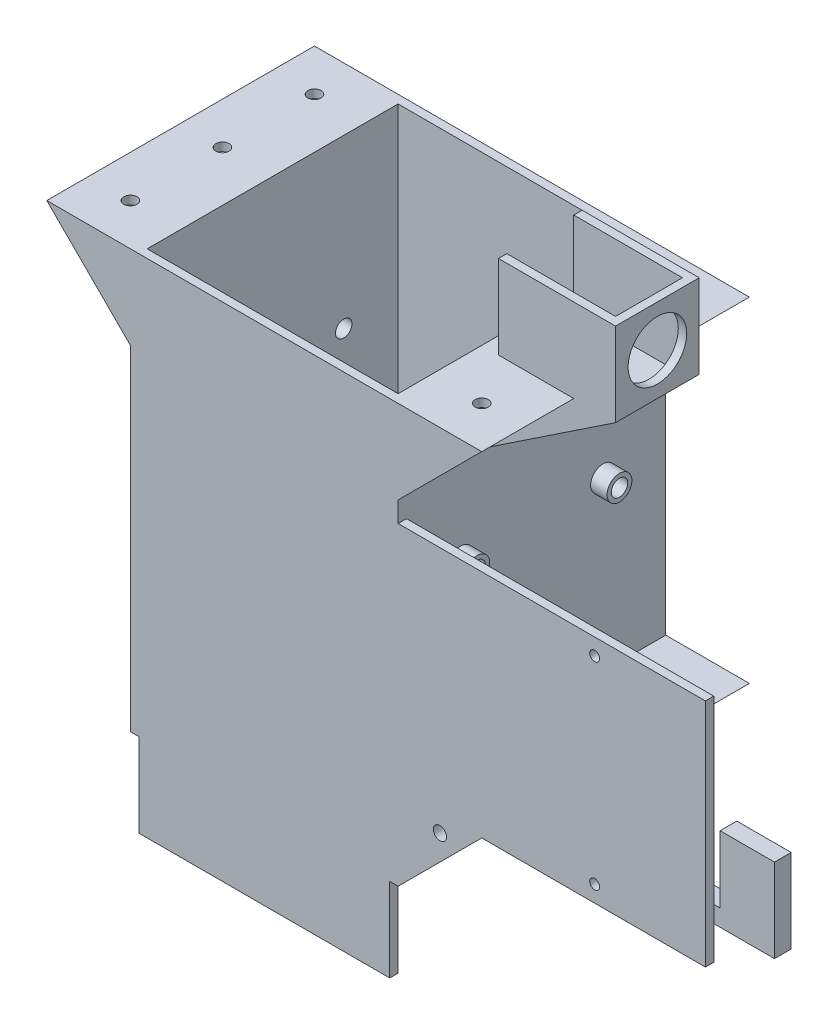
SolidWorks part; units mm, degrees
ref_plane "Front Plane" through (0, 0, 0) normal (0, 0, 1) x (1, 0, 0)
ref_plane "Top Plane" through (0, 0, 0) normal (0, 1, 0) x (1, 0, 0)
ref_plane "Right Plane" through (0, 0, 0) normal (1, 0, 0) x (0, 0, -1)
sketch "Sketch1" plane through (0, 0, 0) normal (0, 1, 0) x (1, 0, 0)
  line L1 (0, 0) -> (81.28, 0)
  line L2 (0, 0) -> (0, 81.28)
  line L3 (0, 81.28) -> (81.28, 81.28)
  line L4 (81.28, 0) -> (81.28, 81.28)
  line L5 (2.54, 2.54) -> (78.74, 2.54)
  line L6 (2.54, 2.54) -> (2.54, 78.74)
  line L7 (2.54, 78.74) -> (78.74, 78.74)
  line L8 (78.74, 2.54) -> (78.74, 78.74)
  dimension "D1" = 2.54
  dimension "D2" = 2.54
  dimension "D3" = 2.54
  dimension "D4" = 2.54
  dimension "D5" = 76.2
  dimension "D6" = 76.2
extrude "Boss-Extrude1" add sketch "Sketch1" along normal blind 177.8
sketch "Sketch2" plane through (0, 0, 0) normal (1, 0, 0) x (0, 0, -1)
  line L0 (109.0297, 38.1) -> (-23.7268, 38.1) construction
  line L1 (81.28, 0) -> (0, 0) construction
  line L2 (40.64, -8.2418) -> (40.64, 63.9342) construction
  line L3 (81.28, 177.8) -> (81.28, 0) construction
  line L5 (66.04, 0) -> (63.5, 0)
  line L6 (66.04, 0) -> (66.04, 38.1)
  line L7 (66.04, 38.1) -> (63.5, 38.1)
  line L8 (63.5, 0) -> (63.5, 38.1)
  dimension "D1" = 38.1
  dimension "D2" = 40.64
  dimension "D3" = 2.54
  dimension "D4" = 15.24
extrude "Boss-Extrude2" add sketch "Sketch2" against normal blind 25.4
sketch "Sketch3" plane through (0, 0, 0) normal (0, 0, 1) x (1, 0, 0)
  line L1 (81.28, 0) -> (78.74, 0)
  line L2 (81.28, 0) -> (81.28, 25.4)
  line L3 (81.28, 25.4) -> (78.74, 25.4)
  line L4 (78.74, 0) -> (78.74, 25.4)
  dimension "D1" = 2.54
  dimension "D2" = 25.4
extrude "Cut-Extrude1" cut sketch "Sketch3" against normal through all
sketch "Sketch7" plane through (0, 0, 0) normal (0, 0, 1) x (1, 0, 0)
  line L0 (81.28, 25.4) -> (106.68, 50.8)
  line L1 (106.68, 50.8) -> (81.28, 50.8)
  line L2 (81.28, 177.8) -> (81.28, 25.4) construction
  line L3 (81.28, 50.8) -> (81.28, 25.4)
  dimension "D1" = 45
  dimension "D2" = 25.4
extrude "Boss-Extrude3" add sketch "Sketch7" against normal blind 12.7
sketch "Sketch10" plane through (0, 0, -81.28) normal (0, 0, -1) x (-1, 0, 0)
  line L0 (-81.28, 25.4) -> (-81.28, 50.8)
  line L1 (-81.28, 177.8) -> (-81.28, 25.4) construction
  line L2 (-81.28, 50.8) -> (-106.68, 50.8)
  line L3 (-106.68, 50.8) -> (-81.28, 25.4)
  dimension "D1" = 45
  dimension "D2" = 25.4
extrude "Boss-Extrude4" add sketch "Sketch10" against normal blind 12.7
sketch "Sketch14" plane through (81.28, 0, 0) normal (1, 0, 0) x (0, 0, -1)
  line L0 (38.1, 50.8) -> (38.1, 25.4)
  line L1 (68.58, 25.4) -> (12.7, 25.4) construction
  line L2 (38.1, 25.4) -> (43.18, 25.4)
  line L3 (43.18, 25.4) -> (43.18, 50.8)
  line L4 (43.18, 50.8) -> (38.1, 50.8)
  line L5 (68.58, 50.8) -> (68.58, 25.4) construction
  dimension "D1" = 5.08
  dimension "D2" = 25.4
  dimension "D3" = 25.4
extrude "Boss-Extrude6" add sketch "Sketch14" along normal blind 76.2
sketch "Sketch16" plane through (0, 0, -38.1) normal (0, 0, 1) x (1, 0, 0)
  line L0 (157.48, 50.8) -> (81.28, 50.8) construction
  line L1 (140.97, 50.8) -> (116.84, 50.8)
  line L2 (140.97, 50.8) -> (140.97, 30.48)
  line L3 (140.97, 30.48) -> (116.84, 30.48)
  line L4 (116.84, 50.8) -> (116.84, 30.48)
  line L5 (157.48, 50.8) -> (157.48, 25.4) construction
  line L6 (157.48, 25.4) -> (81.28, 25.4) construction
  dimension "D1" = 16.51
  dimension "D2" = 24.13
  dimension "D3" = 5.08
extrude "Cut-Extrude2" cut sketch "Sketch16" against normal up to next
sketch "Sketch17" plane through (0, 0, -38.1) normal (0, 0, 1) x (1, 0, 0)
  line L0 (113.03, 59.2483) -> (113.03, 15.3249) construction
  line L1 (116.84, 50.8) -> (116.84, 30.48) construction
  line L2 (116.84, 50.8) -> (81.28, 50.8) construction
  line L3 (113.792, 48.26) -> (115.824, 48.26)
  line L4 (113.792, 48.26) -> (113.792, 33.02)
  line L5 (113.792, 33.02) -> (115.824, 33.02)
  line L6 (115.824, 48.26) -> (115.824, 33.02)
  line L7 (141.732, 48.26) -> (143.764, 48.26)
  line L8 (141.732, 48.26) -> (141.732, 33.02)
  line L9 (141.732, 33.02) -> (143.764, 33.02)
  line L10 (143.764, 48.26) -> (143.764, 33.02)
  line L11 (116.84, 30.48) -> (116.84, 62.58) construction
  line L12 (116.84, 30.48) -> (140.97, 30.48) construction
  line L14 (140.97, 30.48) -> (140.97, 50.8) construction
  dimension "D1" = 3.81
  dimension "D2" = 2.54
  dimension "D3" = 2.54
  dimension "D4" = 0.762
  dimension "D5" = 2.032
  dimension "D6" = 2.032
  dimension "D7" = 0.762
extrude "Cut-Extrude3" [suppressed] cut sketch "Sketch17" against normal up to next
sketch "Sketch22" plane through (0, 0, 0) normal (0, 0, 1) x (1, 0, 0)
  line L0 (93.98, 45.72) -> (101.6, 45.72) construction
  line L1 (106.68, 50.8) -> (81.28, 50.8) construction
  line L2 (93.98, 50.8) -> (93.98, 45.72) construction
  line L4 (81.28, 25.4) -> (106.68, 50.8) construction
  circle A0 centre (93.98, 45.72) radius 2
  point P0 (93.98, 50.8)
  point P10 (93.98, 38.1)
  point P11 (93.2178, 45.72)
  dimension "D3" = 4
  dimension "D1" = 5.08
  dimension "D2" = 12.7
extrude "Cut-Extrude6" cut sketch "Sketch22" against normal through all
sketch "Sketch28" plane through (81.28, 0, 0) normal (1, 0, 0) x (0, 0, -1)
  line L0 (40.64, 175.678) -> (40.64, 120.0937) construction
  line L1 (40.64, 184.0271) -> (40.64, -14.0592) construction
  line L2 (0, 177.8) -> (81.28, 177.8) construction
  line L3 (0, 177.8) -> (0, 50.8) construction
  line L5 (53.34, 177.8) -> (27.94, 177.8)
  line L6 (53.34, 177.8) -> (53.34, 127)
  line L7 (53.34, 127) -> (27.94, 127)
  line L8 (27.94, 177.8) -> (27.94, 127)
  line L9 (53.34, 177.8) -> (27.94, 127) construction
  line L10 (53.34, 127) -> (27.94, 177.8) construction
  point P8 (40.64, 109.22)
  dimension "D2" = 40.64
  dimension "D3" = 50.8
  dimension "D4" = 25.4
extrude "Boss-Extrude7" add sketch "Sketch28" along normal blind 38.1
sketch "Sketch30" plane through (0, 0, -27.94) normal (0, 0, 1) x (1, 0, 0)
  line L0 (81.28, 127) -> (119.38, 127)
  line L1 (119.38, 127) -> (119.38, 152.4)
  line L3 (119.38, 152.4) -> (81.28, 127)
  dimension "D1" = 25.4
  dimension "D2" = 33.69
extrude "Cut-Extrude8" cut sketch "Sketch30" against normal up to next
sketch "Sketch32" plane through (0, 177.8, 0) normal (0, 1, 0) x (1, 0, 0)
  line L0 (119.38, 53.34) -> (81.28, 53.34) construction
  line L1 (83.82, 50.8) -> (116.84, 50.8)
  line L2 (83.82, 50.8) -> (83.82, 30.48)
  line L3 (83.82, 30.48) -> (116.84, 30.48)
  line L4 (116.84, 50.8) -> (116.84, 30.48)
  line L5 (83.82, 50.8) -> (116.84, 30.48) construction
  line L6 (83.82, 30.48) -> (116.84, 50.8) construction
  line L7 (119.38, 53.34) -> (119.38, 27.94) construction
  line L8 (119.38, 27.94) -> (81.28, 27.94) construction
  line L9 (81.28, 53.34) -> (81.28, 81.28) construction
  point P0 (100.33, 40.64)
  dimension "D1" = 2.54
  dimension "D2" = 2.54
  dimension "D3" = 2.54
  dimension "D4" = 2.54
extrude "Cut-Extrude9" cut sketch "Sketch32" against normal blind 25.4
sketch "Sketch34" plane through (119.38, 0, 0) normal (1, 0, 0) x (0, 0, -1)
  line L0 (40.64, 147.7754) -> (40.64, 78.4323) construction
  line L1 (11.6001, 165.1) -> (93.4551, 165.1) construction
  line L2 (27.94, 177.8) -> (27.94, 152.4) construction
  line L3 (53.34, 177.8) -> (27.94, 177.8) construction
  circle A0 centre (40.64, 165.1) radius 8.89
  dimension "D3" = 17.78
  dimension "D1" = 12.7
  dimension "D2" = 12.7
extrude "Cut-Extrude13" cut sketch "Sketch34" against normal up to surface (40.64 mm away) up to face at (78.74, 101.6, -40.64)
sketch "Sketch37" plane through (0, 0, -63.5) normal (0, 0, 1) x (1, 0, 0)
  line L0 (-25.4, 38.1) -> (0, 38.1)
  line L1 (0, 38.1) -> (0, 52.7647)
  line L2 (0, 52.7647) -> (-25.4, 38.1)
  dimension "D1" = 30
extrude "Boss-Extrude9" add sketch "Sketch37" against normal up to surface (2.54 mm away) up to face at (-12.7, 19.05, -66.04)
sketch "Sketch38" plane through (0, 0, 0) normal (0, 0, 1) x (1, 0, 0)
  line L1 (0, 0) -> (2.54, 0)
  line L2 (0, 0) -> (0, 25.4)
  line L3 (0, 25.4) -> (2.54, 25.4)
  line L4 (2.54, 0) -> (2.54, 25.4)
  point P5 (0, 0)
  dimension "D1" = 25.4
  dimension "D2" = 2.54
extrude "Cut-Extrude15" cut sketch "Sketch38" against normal up to surface (63.5 mm away) up to face at (-12.7, 22.7162, -63.5)
sketch "Sketch40" plane through (81.28, 0, 0) normal (1, 0, 0) x (0, 0, -1)
  line L0 (-23.3344, 101.6) -> (103.8421, 101.6) construction
  line L1 (38.1, 25.4) -> (12.7, 25.4) construction
  line L2 (19.05, 177.8) -> (19.05, 25.4) construction
  line L3 (62.23, 177.8) -> (62.23, 25.4) construction
  line L6 (0, 177.8) -> (0, 50.8) construction
  line L7 (81.28, 177.8) -> (81.28, 50.8) construction
  line L8 (0, 177.8) -> (27.94, 177.8) construction
  line L9 (53.34, 177.8) -> (81.28, 177.8) construction
  line L10 (68.58, 25.4) -> (43.18, 25.4) construction
  circle A0 centre (19.05, 101.6) radius 2.5
  circle A1 centre (62.23, 101.6) radius 2.5
  point P16 (19.05, 177.8)
  point P19 (62.23, 177.8)
  point P22 (19.05, 25.4)
  point P23 (62.23, 25.4)
  dimension "D4" = 5
  dimension "D5" = 5
  dimension "D1" = 76.2
  dimension "D2" = 19.05
  dimension "D3" = 19.05
extrude "Cut-Extrude17" cut sketch "Sketch40" against normal up to surface (81.28 mm away) up to face at (0, 63.9912, -52.705)
sketch "Sketch41" plane through (81.28, 0, 0) normal (1, 0, 0) x (0, 0, -1)
  circle A0 centre (19.05, 101.6) radius 3.77
  circle A1 centre (19.05, 101.6) radius 2.5
  circle A2 centre (62.23, 101.6) radius 3.77
  circle A4 centre (62.23, 101.6) radius 2.5
  dimension "D1" = 1.27
  dimension "D2" = 1.27
extrude "Boss-Extrude10" add sketch "Sketch41" along normal blind 5
sketch "Sketch42" plane through (0, 0, 0) normal (-1, 0, 0) x (0, 0, 1)
  circle A0 centre (-62.23, 101.6) radius 2.5
  circle A1 centre (-62.23, 101.6) radius 3.77
  circle A2 centre (-19.05, 101.6) radius 2.5
  circle A3 centre (-19.05, 101.6) radius 3.77
  dimension "D1" = 1.27
  dimension "D2" = 1.27
extrude "Boss-Extrude11" add sketch "Sketch42" along normal blind 5
sketch "Sketch43" plane through (0, 177.8, 0) normal (0, 1, 0) x (1, 0, 0)
  line L1 (83.82, 53.34) -> (83.82, 27.94)
  line L3 (78.74, 2.54) -> (2.54, 2.54)
  line L4 (2.54, 2.54) -> (78.74, 2.54) construction
  line L5 (2.54, 2.54) -> (2.54, 78.74)
  line L6 (2.54, 78.74) -> (78.74, 78.74)
  line L11 (81.28, 81.28) -> (0, 81.28)
  line L12 (0, 81.28) -> (0, 0)
  line L13 (0, 0) -> (81.28, 0)
  line L19 (81.28, 81.28) -> (81.28, 53.34)
  line L21 (81.28, 53.34) -> (83.82, 53.34)
  line L22 (81.28, 0) -> (81.28, 27.94)
  line L23 (81.28, 27.94) -> (83.82, 27.94)
  line L24 (78.74, 78.74) -> (78.74, 2.54)
  line L25 (83.82, 50.8) -> (83.82, 30.48) construction
  line L26 (119.38, 27.94) -> (81.28, 27.94) construction
  line L27 (81.28, 81.28) -> (0, 81.28) construction
  point P3 (81.28, 53.34)
  point P4 (83.82, 53.34)
  point P15 (83.82, 27.94)
  point P19 (81.28, 81.28)
  point P25 (81.28, 0)
extrude "Cut-Extrude20" cut sketch "Sketch43" against normal blind 25.4
sketch "Sketch44" plane through (0, 0, 0) normal (0, 0, 1) x (1, 0, 0)
  line L0 (0, 152.4) -> (0, 25.4) construction
  line L1 (0, 50.8) -> (174.6, 50.8)
  line L2 (0, 50.8) -> (0, 120.8)
  line L3 (0, 120.8) -> (174.6, 120.8)
  line L4 (174.6, 50.8) -> (174.6, 120.8)
  line L5 (106.68, 50.8) -> (81.28, 50.8) construction
  line L6 (-25.4, 38.1) -> (-25.4, 0) construction
  line L7 (140.97, 50.8) -> (140.97, 120.8) construction
  line L8 (140.97, 30.48) -> (140.97, 50.8) construction
  circle A0 centre (140.97, 115.8) radius 1.5
  circle A1 centre (140.97, 55.8) radius 1.5
  dimension "D3" = 3
  dimension "D1" = 200
  dimension "D2" = 70
  dimension "D4" = 60
  dimension "D5" = 5
extrude "Boss-Extrude12" add sketch "Sketch44" against normal blind 2.54
sketch "Sketch45" plane through (0, 0, 0) normal (0, 0, 1) x (1, 0, 0)
  line L0 (0, 152.4) -> (-25.4, 152.4)
  line L1 (-25.4, 152.4) -> (0, 127)
  line L2 (0, 152.4) -> (0, 25.4) construction
  line L3 (0, 127) -> (0, 152.4)
  point P6 (-20.8806, 152.4)
  point P7 (-38.2091, 152.4)
  dimension "D1" = 25.4
  dimension "D2" = 45
extrude "Boss-Extrude13" add sketch "Sketch45" against normal blind 2.54
sketch "Sketch46" plane through (0, 0, -81.28) normal (0, 0, -1) x (-1, 0, 0)
  line L0 (0, 152.4) -> (0, 127)
  line L1 (0, 127) -> (25.4, 152.4)
  line L2 (25.4, 152.4) -> (0, 152.4)
extrude "Boss-Extrude14" add sketch "Sketch46" against normal blind 2.54
sketch "Sketch47" plane through (0, 0, 0) normal (0, 0, 1) x (1, 0, 0)
  line L0 (0, 152.4) -> (-25.4, 152.4)
  line L1 (-25.4, 152.4) -> (81.28, 152.4) construction
  line L2 (-25.4, 152.4) -> (-22.86, 149.86)
  line L3 (-25.4, 152.4) -> (0, 127) construction
  line L4 (-22.86, 149.86) -> (0, 149.86)
  line L5 (0, 149.86) -> (0, 152.4)
  line L6 (0, 127) -> (0, 25.4) construction
  dimension "D1" = 2.54
extrude "Boss-Extrude15" add sketch "Sketch47" against normal through all
sketch "Sketch48" plane through (0, 0, 0) normal (0, 0, 1) x (1, 0, 0)
  line L0 (81.28, 152.4) -> (106.68, 152.4)
  line L1 (106.68, 152.4) -> (81.28, 127)
  line L2 (81.28, 152.4) -> (81.28, 127) construction
  line L3 (81.28, 127) -> (81.28, 152.4)
  dimension "D1" = 25.4
  dimension "D2" = 45
extrude "Boss-Extrude16" add sketch "Sketch48" against normal blind 2.54
sketch "Sketch49" plane through (0, 0, -81.28) normal (0, 0, -1) x (-1, 0, 0)
  line L0 (-81.28, 152.4) -> (-106.68, 152.4)
  line L1 (-106.68, 152.4) -> (-81.28, 127)
  line L2 (-81.28, 127) -> (-81.28, 152.4) construction
  line L3 (-81.28, 127) -> (-81.28, 152.4)
  dimension "D1" = 25.4
  dimension "D2" = 45
extrude "Boss-Extrude17" add sketch "Sketch49" against normal blind 2.54
sketch "Sketch50" plane through (0, 0, -81.28) normal (0, 0, -1) x (-1, 0, 0)
  line L0 (-81.28, 152.4) -> (-106.68, 152.4)
  line L1 (-106.68, 152.4) -> (25.4, 152.4) construction
  line L2 (-106.68, 152.4) -> (-81.28, 127) construction
  line L3 (-106.68, 152.4) -> (-104.14, 149.86)
  line L4 (-104.14, 149.86) -> (-81.28, 149.86)
  line L5 (-81.28, 149.86) -> (-81.28, 152.4)
  line L6 (-81.28, 127) -> (-81.28, 50.8) construction
  dimension "D1" = 2.54
extrude "Boss-Extrude18" add sketch "Sketch50" against normal through all
sketch "Sketch51" plane through (0, 152.4, 0) normal (0, 1, 0) x (1, 0, 0)
  line L0 (-12.7, 81.28) -> (-12.7, 0) construction
  line L1 (-25.4, 0) -> (106.68, 0) construction
  line L2 (106.68, 81.28) -> (-25.4, 81.28) construction
  line L3 (93.98, 0) -> (93.98, 81.28) construction
  line L4 (-25.4, 81.28) -> (-25.4, 0) construction
  line L5 (106.68, 53.34) -> (106.68, 81.28) construction
  line L6 (-25.4003, 68.58) -> (106.68, 68.58) construction
  line L7 (-25.4, 40.64) -> (116.84, 40.64) construction
  line L8 (116.84, 30.48) -> (116.84, 50.8) construction
  line L9 (-25.4, 12.7) -> (106.68, 12.7) construction
  line L10 (106.68, 27.94) -> (106.68, 0) construction
  circle A0 centre (-12.7, 68.58) radius 2
  circle A1 centre (-12.7, 40.64) radius 2
  circle A2 centre (-12.7, 12.7) radius 2
  circle A3 centre (93.98, 68.58) radius 2
  circle A4 centre (93.98, 12.7) radius 2
  point P33 (-12.7, 12.7)
  point P34 (-12.7, 12.7)
  point P35 (106.68, 67.31)
  dimension "D5" = 4
  dimension "D1" = 12.7
  dimension "D2" = 12.7
  dimension "D3" = 12.7
  dimension "D4" = 12.7
extrude "Cut-Extrude21" cut sketch "Sketch51" against normal blind 2.54
